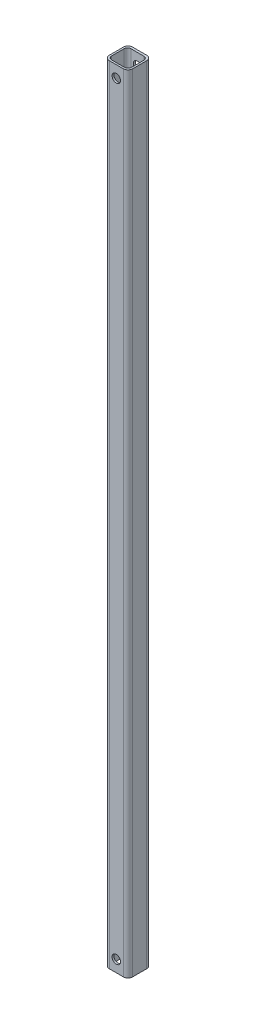
SolidWorks part; units mm, degrees
material "Plain Carbon Steel"
ref_plane "Front Plane" through (0, 0, 0) normal (0, 0, 1) x (1, 0, 0)
ref_plane "Top Plane" through (0, 0, 0) normal (0, 1, 0) x (1, 0, 0)
ref_plane "Right Plane" through (0, 0, 0) normal (1, 0, 0) x (0, 0, -1)
sketch "Sketch1" plane through (0, 0, 0) normal (0, 1, 0) x (1, 0, 0)
  line L0 (-8.6995, -13.462) -> (8.6995, -13.462)
  line L1 (-13.462, -8.6995) -> (-13.462, 8.0645)
  line L2 (8.6995, 12.827) -> (-8.6995, 12.827)
  line L3 (13.462, 8.0645) -> (13.462, -8.6995)
  line L4 (-9.525, -15.875) -> (9.525, -15.875)
  line L5 (-15.875, -9.525) -> (-15.875, 9.525)
  line L6 (9.525, 15.875) -> (-9.525, 15.875)
  line L7 (15.875, 9.525) -> (15.875, -9.525)
  line L8 (0, 12.827) -> (0, -13.462) construction
  arc A0 (15.875, 9.525) -> (9.525, 15.875) centre (9.525, 9.525) ccw
  arc A1 (9.525, -15.875) -> (15.875, -9.525) centre (9.525, -9.525) ccw
  arc A2 (-15.875, -9.525) -> (-9.525, -15.875) centre (-9.525, -9.525) ccw
  arc A3 (-9.525, 15.875) -> (-15.875, 9.525) centre (-9.525, 9.525) ccw
  arc A4 (-8.6995, 12.827) -> (-13.462, 8.0645) centre (-8.6995, 8.0645) ccw
  arc A5 (13.462, 8.0645) -> (8.6995, 12.827) centre (8.6995, 8.0645) ccw
  arc A6 (8.6995, -13.462) -> (13.462, -8.6995) centre (8.6995, -8.6995) ccw
  arc A7 (-13.462, -8.6995) -> (-8.6995, -13.462) centre (-8.6995, -8.6995) ccw
  dimension "D1" = 6.35
  dimension "D2" = 4.7625
  dimension "D3" = 2.413
  dimension "D4" = 3.048
  dimension "D5" = 2.413
  dimension "D6" = 2.413
  dimension "D7" = 31.75
  dimension "D8" = 31.75
extrude "Boss-Extrude1" add sketch "Sketch1" along normal mid plane 1066.8
sketch "Sketch2" plane through (0, 0, 15.875) normal (0, 0, 1) x (1, 0, 0)
  line L0 (-9.525, 533.4) -> (9.525, 533.4) construction
  line L1 (0, -17.4625) -> (0, 17.4625) construction
  circle A0 centre (0, 517.525) radius 5.715
  dimension "D2" = 11.43
  dimension "D1" = 15.875
extrude "Cut-Extrude1" cut sketch "Sketch2" against normal through all
mirror "Mirror1" about plane through (0, 0, 0) normal (0, 1, 0) of "Cut-Extrude1"
